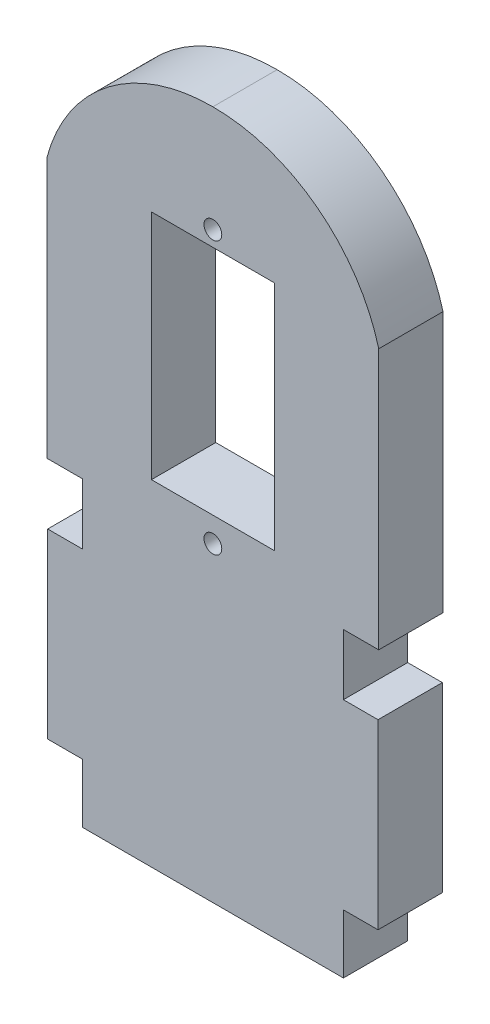
SolidWorks part; units mm, degrees
ref_plane "Front Plane" through (0, 0, 0) normal (0, 0, 1) x (1, 0, 0)
ref_plane "Top Plane" through (0, 0, 0) normal (0, 1, 0) x (1, 0, 0)
ref_plane "Right Plane" through (0, 0, 0) normal (1, 0, 0) x (0, 0, -1)
sketch "Sketch3" plane through (0, 0, 0) normal (0, 0, 1) x (1, 0, 0)
  line L28 (42.7808, 19.2799) -> (42.7808, 92.3065) construction
  line L29 (42.7808, 19.2799) -> (42.7808, 0) construction
  line L30 (42.7808, 0) -> (0, 0) construction
  line L31 (26.0088, 49.7999) -> (26.0088, 76.1663)
  line L32 (29.5808, 49.7999) -> (26.0088, 49.7999)
  line L33 (29.5808, 43.6499) -> (29.5808, 49.7999)
  line L34 (26.0808, 43.6499) -> (29.5808, 43.6499)
  line L35 (26.0808, 25.2499) -> (26.0808, 43.6499)
  line L36 (29.5808, 25.2499) -> (26.0808, 25.2499)
  line L37 (29.5808, 19.2799) -> (29.5808, 25.2499)
  line L38 (36.5723, 76.6618) -> (36.5723, 53.2123)
  line L96 (29.5808, 19.2799) -> (29.5808, 25.2069)
  line L104 (29.5808, 19.2799) -> (55.9808, 19.2799)
  line L105 (55.9808, 19.2799) -> (55.9808, 25.2499)
  line L106 (55.9808, 25.2499) -> (59.4808, 25.2499)
  line L107 (59.4808, 25.2499) -> (59.4808, 43.6499)
  line L108 (59.4808, 43.6499) -> (55.9808, 43.6499)
  line L109 (55.9808, 43.6499) -> (55.9808, 49.7999)
  line L110 (55.9808, 49.7999) -> (59.5528, 49.7999)
  line L111 (59.5528, 49.7999) -> (59.5528, 76.1663)
  line L112 (36.5723, 76.6618) -> (48.9893, 76.6618)
  line L113 (48.9893, 76.6618) -> (48.9893, 53.2123)
  line L114 (48.9893, 53.2123) -> (36.5723, 53.2123)
  arc A14 (59.5528, 76.1663) -> (26.1658, 76.1663) centre (42.8593, 71.682) ccw
  circle A15 centre (42.7808, 50.7123) radius 0.9
  circle A16 centre (42.7808, 78.2123) radius 0.9
  arc A17 (26.0088, 76.1663) -> (59.3958, 76.1663) centre (42.7023, 71.682) cw
  point P16 (36.5723, 64.9371)
  dimension "D1" = 23.4495
  dimension "D2" = 18.4
  dimension "D6" = 1.8
  dimension "D7" = 1.8
  dimension "D3" = 25
  dimension "D4" = 2.5
  dimension "D5" = 33.9324
  dimension "D8" = 42.7808
  dimension "D9" = 19.2799
  dimension "D10" = 5.97
  dimension "D11" = 3.5
  dimension "D12" = 6.15
  dimension "D13" = 13.2
extrude "Boss-Extrude6" add sketch "Sketch3" along normal blind 6.5 separate body
